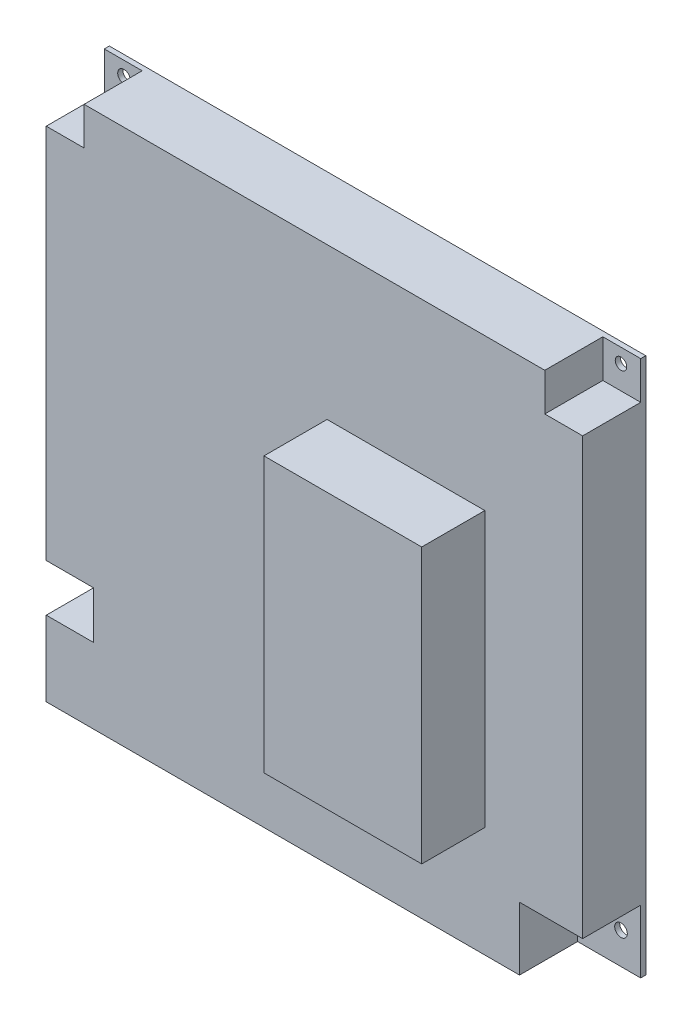
SolidWorks part; units mm, degrees
ref_plane "前基準面" through (0, 0, 0) normal (0, 0, 1) x (1, 0, 0)
ref_plane "上基準面" through (0, 0, 0) normal (0, 1, 0) x (1, 0, 0)
ref_plane "右基準面" through (0, 0, 0) normal (1, 0, 0) x (0, 0, -1)
sketch "草圖1" plane through (0, 0, 0) normal (0, 0, 1) x (1, 0, 0)
  line L1 (-85, 85) -> (85, 85)
  line L2 (-85, 85) -> (-85, -85)
  line L3 (-85, -85) -> (85, -85)
  line L4 (85, 85) -> (85, -85)
  point P4 (0, 85)
  point P6 (85, 0)
  dimension "D1" = 170
  dimension "D2" = 170
extrude "填料-伸長1" add sketch "草圖1" along normal blind 20
sketch "草圖2" plane through (0, 0, 20) normal (0, 0, 1) x (1, 0, 0)
  line L0 (85, -85) -> (85, 85) construction
  line L1 (65, -65) -> (85, -65)
  line L2 (65, -65) -> (65, -85)
  line L3 (65, -85) -> (85, -85)
  line L4 (85, -65) -> (85, -85)
  line L5 (-85, -85) -> (85, -85) construction
  line L6 (-85, 85) -> (-85, -85) construction
  line L7 (73, 85) -> (85, 85)
  line L8 (73, 85) -> (73, 73)
  line L9 (73, 73) -> (85, 73)
  line L10 (85, 85) -> (85, 73)
  line L11 (-85, 85) -> (-73, 85)
  line L12 (-85, 85) -> (-85, 73)
  line L13 (-85, 73) -> (-73, 73)
  line L14 (-73, 85) -> (-73, 73)
  line L15 (85, 85) -> (-85, 85) construction
  line L17 (-85, -46.2117) -> (-70, -46.2117)
  line L18 (-85, -46.2117) -> (-85, -61.2117)
  line L19 (-85, -61.2117) -> (-70, -61.2117)
  line L20 (-70, -46.2117) -> (-70, -61.2117)
  dimension "D1" = 20
  dimension "D2" = 20
  dimension "D3" = 12
  dimension "D4" = 12
  dimension "D5" = 12
  dimension "D6" = 12
  dimension "D7" = 15
  dimension "D8" = 15
extrude "除料-伸長1" cut sketch "草圖2" against normal blind 18.4
sketch "草圖3" plane through (0, 0, 1.6) normal (0, 0, 1) x (1, 0, 0)
  line L0 (65, -85) -> (85, -85) construction
  line L1 (85, -85) -> (85, -65) construction
  line L5 (-78.75, 80.5) -> (78.75, 80.5) construction
  line L6 (73, 85) -> (-73, 85) construction
  line L7 (-85, 85) -> (-85, -85) construction
  line L8 (85, 73) -> (85, 85) construction
  line L9 (85, 85) -> (73, 85) construction
  circle A0 centre (78.75, -75) radius 2
  circle A1 centre (78.75, 80.5) radius 1.8227
  circle A2 centre (-78.75, 80.5) radius 2
  circle A3 centre (-78.75, -51.5) radius 2
  point P10 (0, 80.5)
  point P13 (0, 85)
  dimension "D1" = 10
  dimension "D3" = 157.5
  dimension "D4" = 6.25
  dimension "D7" = 132
  dimension "D2" = 6.25
  dimension "D5" = 6.25
  dimension "D6" = 4.5
extrude "除料-伸長2" cut sketch "草圖3" against normal blind 18.4
sketch "草圖4" plane through (0, 0, 20) normal (0, 0, 1) x (1, 0, 0)
  line L0 (85, -65) -> (85, 73) construction
  line L1 (4, 37) -> (54, 37)
  line L2 (4, 37) -> (4, -50)
  line L3 (4, -50) -> (54, -50)
  line L4 (54, 37) -> (54, -50)
  line L5 (-85, -85) -> (65, -85) construction
  line L6 (73, 85) -> (-73, 85) construction
  line L7 (-85, 73) -> (-85, -46.2117) construction
  dimension "D1" = 31
  dimension "D2" = 35
  dimension "D3" = 48
  dimension "D4" = 89
extrude "填料-伸長2" add sketch "草圖4" along normal blind 20
